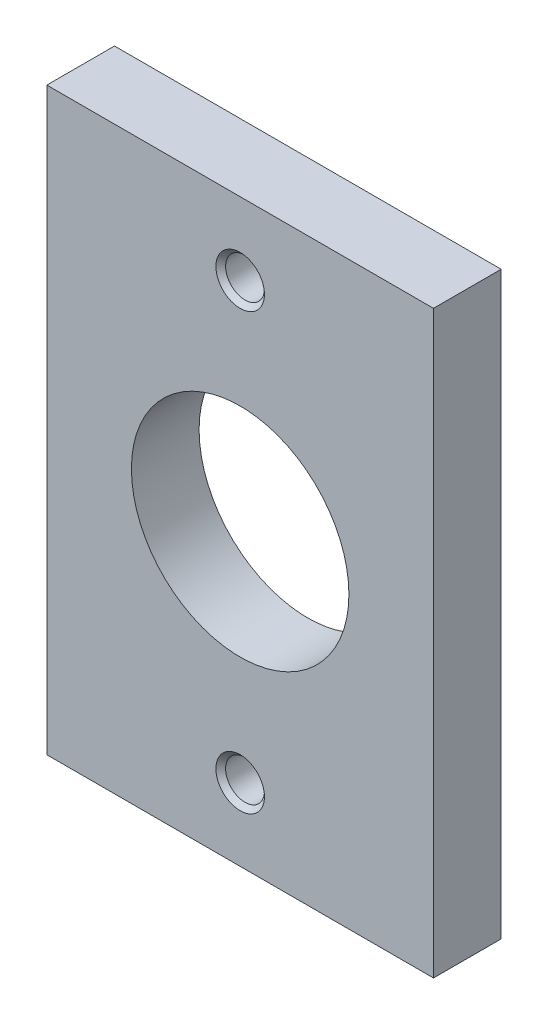
SolidWorks part; units mm, degrees
material "1060 Alloy"
ref_plane "Front Plane" through (0, 0, 0) normal (0, 0, 1) x (1, 0, 0)
ref_plane "Top Plane" through (0, 0, 0) normal (0, 1, 0) x (1, 0, 0)
ref_plane "Right Plane" through (0, 0, 0) normal (1, 0, 0) x (0, 0, -1)
sketch "Sketch1" plane through (0, 0, 0) normal (0, 0, 1) x (1, 0, 0)
  line L1 (0, 0) -> (50.8, 0)
  line L2 (0, 0) -> (0, 76.2)
  line L3 (0, 76.2) -> (50.8, 76.2)
  line L4 (50.8, 0) -> (50.8, 76.2)
  circle A0 centre (25.4, 38.1) radius 14.2875
  dimension "D3" = 28.575
  dimension "D1" = 50.8
  dimension "D2" = 76.2
  dimension "D4" = 25.4
  dimension "D5" = 38.1
extrude "Boss-Extrude1" add sketch "Sketch1" along normal blind 8.89
hole_wizard "#10 Clearance Hole1" positions "Sketch3" profile "Sketch2" hole size "#10" standard "ANSI Inch" end condition through all
sketch "Sketch3" plane through (0, 0, 8.89) normal (0, 0, 1) x (1, 0, 0)
  line L1 (25.4, 66.675) -> (25.4, 76.2) construction
  line L2 (50.8, 76.2) -> (0, 76.2) construction
  line L5 (25.4, 9.525) -> (25.4, 0) construction
  line L6 (0, 0) -> (50.8, 0) construction
  point P0 (25.4, 66.675)
  point P2 (25.4, 9.525)
  dimension "D1" = 57.15
sketch "Sketch2" plane through (25.4, 66.675, 8.89) normal (1, 0, 0) x (0, -1, 0)
  line L0 (0, 0) -> (0, 8.89)
  line L1 (0, 8.89) -> (2.5527, 8.89)
  line L2 (2.5527, 8.89) -> (2.5527, 0.635)
  line L3 (2.5527, 0.635) -> (3.1877, 0)
  line L5 (3.1877, 0) -> (0, 0)
  line L6 (-2.5527, 0.635) -> (-3.1877, 0) construction
  line L11 (0, -6.35) -> (0, 107.95) construction
  dimension "Thru Hole Dia." = 5.1054
  dimension "Thru Hole Depth" = 8.89
  dimension "Near C'Sink Dia." = 6.3754
  dimension "Near C'Sink Angle" = 90
